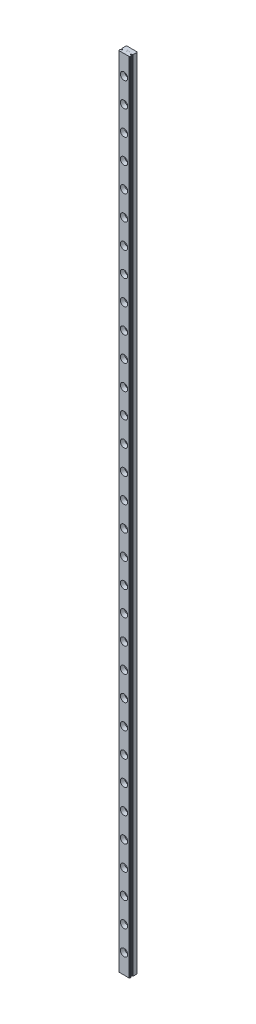
SolidWorks part; units mm, degrees
material "acero"
ref_plane "Alzado" through (0, 0, 0) normal (0, 0, 1) x (1, 0, 0)
ref_plane "Planta" through (0, 0, 0) normal (0, 1, 0) x (1, 0, 0)
ref_plane "Vista lateral" through (0, 0, 0) normal (1, 0, 0) x (0, 0, -1)
ref_plane "Plano1" through (0, 0, 0) normal (0, -1, 0) x (1, 0, 0)
sketch "Croquis1" plane through (0, 0, 0) normal (0, -1, 0) x (1, 0, 0)
  line L0 (4.5, 0) -> (4.5, 6.0117)
  line L1 (4.5, 6.0117) -> (4.1, 6.5)
  line L2 (4.1, 6.5) -> (-4.1, 6.5)
  line L3 (-4.1, 6.5) -> (-4.5, 6.0117)
  line L4 (-4.5, 6.0117) -> (-4.5, 0)
  line L5 (-4.5, 0) -> (4.5, 0)
extrude "Saliente-Extruir1" add sketch "Croquis1" against normal blind 652
sketch "Croquis2" plane through (0, 652, 0) normal (0, 1, 0) x (-1, 0, 0)
  line L0 (-4.5, 4.8802) -> (-4.5, 4.0315)
  line L1 (-4.5, 4.0315) -> (-3.8193, 4.0315)
  line L2 (-3.8193, 4.8802) -> (-4.5, 4.8802)
  arc A1 (-3.8193, 4.0315) -> (-3.8193, 4.8802) centre (-3.6695, 4.4558) ccw
  dimension "D4" = 0.9
  dimension "D2" = 0.8487
extrude "Cortar-Extruir1" cut sketch "Croquis2" against normal through all
sketch "Croquis3" plane through (0, 652, 0) normal (0, 1, 0) x (-1, 0, 0)
  line L0 (-4.0265, 4.0315) -> (-4.5, 4.0315)
  line L1 (-4.5, 4.0315) -> (-4.5, 3.5836)
  arc A0 (-4.5, 3.5836) -> (-4.0265, 4.0315) centre (-4.8765, 4.4558) ccw
extrude "Cortar-Extruir2" cut sketch "Croquis3" against normal through all
sketch "Croquis4" plane through (0, 652, 0) normal (0, 1, 0) x (-1, 0, 0)
  line L0 (-4.5, 5.3281) -> (-4.5, 4.8802)
  line L1 (-4.5, 4.8802) -> (-4.0265, 4.8802)
  arc A0 (-4.0265, 4.8802) -> (-4.5, 5.3281) centre (-4.8765, 4.4558) ccw
extrude "Cortar-Extruir3" cut sketch "Croquis4" against normal through all
sketch "Croquis5" plane through (0, 652, 0) normal (0, 1, 0) x (-1, 0, 0)
  line L0 (4.5, 4.0315) -> (4.5, 4.8802)
  line L1 (4.5, 4.8802) -> (3.8193, 4.8802)
  line L2 (3.8193, 4.0315) -> (4.5, 4.0315)
  arc A1 (3.8193, 4.8802) -> (3.8193, 4.0315) centre (3.6695, 4.4558) ccw
  dimension "D3" = 0.9
  dimension "D2" = 0.8487
extrude "Cortar-Extruir4" cut sketch "Croquis5" against normal through all
sketch "Croquis6" plane through (0, 652, 0) normal (0, 1, 0) x (-1, 0, 0)
  line L0 (4.0265, 4.8802) -> (4.5, 4.8802)
  line L1 (4.5, 4.8802) -> (4.5, 5.3281)
  arc A0 (4.5, 5.3281) -> (4.0265, 4.8802) centre (4.8765, 4.4558) ccw
extrude "Cortar-Extruir5" cut sketch "Croquis6" against normal through all
sketch "Croquis7" plane through (0, 652, 0) normal (0, 1, 0) x (-1, 0, 0)
  line L0 (4.5, 3.5836) -> (4.5, 4.0315)
  line L1 (4.5, 4.0315) -> (4.0265, 4.0315)
  arc A0 (4.0265, 4.0315) -> (4.5, 3.5836) centre (4.8765, 4.4558) ccw
extrude "Cortar-Extruir6" cut sketch "Croquis7" against normal through all
sketch "Croquis8" plane through (0, 652, 0) normal (0, 1, 0) x (-1, 0, 0)
  line L0 (0.8914, 3.4037) -> (0.7147, 3.1682)
  line L1 (0.7147, 3.1682) -> (0.2187, 2.611)
  line L2 (0.2187, 2.611) -> (1.0946, 2.6111)
  line L3 (1.0946, 2.6111) -> (1.0946, 2.696)
  line L4 (1.0946, 2.696) -> (0.3987, 2.696)
  line L5 (0.3987, 2.696) -> (0.7943, 3.1495)
  line L6 (0.7943, 3.1495) -> (0.9743, 3.3891)
  line L7 (0.9743, 3.3891) -> (1.0671, 3.5734)
  line L8 (1.0671, 3.5734) -> (0.9541, 3.8023)
  line L9 (0.9541, 3.8023) -> (0.7877, 3.8851)
  line L10 (0.7877, 3.8851) -> (0.543, 3.8851)
  line L11 (0.543, 3.8851) -> (0.3754, 3.8036)
  line L12 (0.3754, 3.8036) -> (0.295, 3.6384)
  line L13 (0.295, 3.6384) -> (0.295, 3.562)
  line L14 (0.295, 3.562) -> (0.3813, 3.562)
  line L15 (0.3813, 3.562) -> (0.3813, 3.6318)
  line L16 (0.3813, 3.6318) -> (0.4377, 3.7436)
  line L17 (0.4377, 3.7436) -> (0.5496, 3.8001)
  line L18 (0.5496, 3.8001) -> (0.7802, 3.8001)
  line L19 (0.7802, 3.8001) -> (0.893, 3.7438)
  line L20 (0.893, 3.7438) -> (0.9762, 3.576)
  line L21 (0.9762, 3.576) -> (0.8914, 3.4037)
extrude "Cortar-Extruir7" cut sketch "Croquis8" against normal blind 0.0022
sketch "Croquis9" plane through (0, 0, 0) normal (0, -1, 0) x (1, 0, 0)
  line L0 (-0.2146, 3.8851) -> (-0.954, 3.8851)
  line L1 (-0.954, 3.8851) -> (-0.954, 2.6111)
  line L2 (-0.954, 2.6111) -> (-0.2146, 2.6111)
  line L3 (-0.2146, 2.6111) -> (-0.2146, 2.696)
  line L4 (-0.2146, 2.696) -> (-0.869, 2.696)
  line L5 (-0.869, 2.696) -> (-0.869, 3.2056)
  line L6 (-0.869, 3.2056) -> (-0.5124, 3.2056)
  line L7 (-0.5124, 3.2056) -> (-0.5124, 3.2905)
  line L8 (-0.5124, 3.2905) -> (-0.869, 3.2905)
  line L9 (-0.869, 3.2905) -> (-0.869, 3.8001)
  line L10 (-0.869, 3.8001) -> (-0.2146, 3.8001)
  line L11 (-0.2146, 3.8001) -> (-0.2146, 3.8851)
extrude "Cortar-Extruir8" cut sketch "Croquis9" against normal blind 0.0022
sketch "Croquis10" plane through (0, 652, 0) normal (0, 1, 0) x (-1, 0, 0)
  line L0 (-0.2146, 3.8851) -> (-0.954, 3.8851)
  line L1 (-0.954, 3.8851) -> (-0.954, 2.6111)
  line L2 (-0.954, 2.6111) -> (-0.2146, 2.6111)
  line L3 (-0.2146, 2.6111) -> (-0.2146, 2.696)
  line L4 (-0.2146, 2.696) -> (-0.869, 2.696)
  line L5 (-0.869, 2.696) -> (-0.869, 3.2056)
  line L6 (-0.869, 3.2056) -> (-0.5124, 3.2056)
  line L7 (-0.5124, 3.2056) -> (-0.5124, 3.2905)
  line L8 (-0.5124, 3.2905) -> (-0.869, 3.2905)
  line L9 (-0.869, 3.2905) -> (-0.869, 3.8001)
  line L10 (-0.869, 3.8001) -> (-0.2146, 3.8001)
  line L11 (-0.2146, 3.8001) -> (-0.2146, 3.8851)
extrude "Cortar-Extruir9" cut sketch "Croquis10" against normal blind 0.0022
sketch "Croquis11" plane through (0, 0, 0) normal (0, -1, 0) x (1, 0, 0)
  line L0 (0.5101, 3.6208) -> (0.6071, 3.7187)
  line L1 (0.6071, 3.7187) -> (0.6071, 2.6094)
  line L2 (0.6071, 2.6094) -> (0.692, 2.6094)
  line L3 (0.692, 2.6094) -> (0.692, 3.8834)
  line L4 (0.692, 3.8834) -> (0.6741, 3.8834)
  line L5 (0.6741, 3.8834) -> (0.6741, 3.7951)
  line L6 (0.6741, 3.7951) -> (0.3691, 3.6407)
  line L7 (0.3691, 3.6407) -> (0.3691, 3.5513)
  line L8 (0.3691, 3.5513) -> (0.5101, 3.6208)
extrude "Cortar-Extruir10" cut sketch "Croquis11" against normal blind 0.0022
draft "Ángulo de salida1" type of draft neutral plane draft angle 45.147 faces to draft 1 face at (0.6741, 0.0011, 3.8392) neutral plane through (0.692, 0.0022, 3.8834) neutral plane normal (0, 0, -1) parameters "D1"=45.147
chamfer "Chaflán1" distance 0.4 angle 45 2 edges at (4.5, 326, 0) (-4.5, 326, 0)
fillet "Redondeo1" radius 0.13 8 edges at (4.5, 326, 3.5836) (4.0265, 326, 4.0315) (-4.0265, 326, 4.0315) (-4.0265, 326, 4.8802) (-4.5, 326, 5.3281) (-4.5, 326, 3.5836) (4.5, 326, 5.3281) (4.0265, 326, 4.8802)
hole_wizard "Taladro roscado M3.5x0.61" positions "Croquis35" profile "Croquis34" tap size "M3.5x0.6" standard "Ansi Metric"
sketch "Croquis35" plane through (0, 0, 0) normal (0, 0, -1) x (-1, 0, 0)
  line L3 (0, -8.7858) -> (0, 652) construction
  line L5 (-4.1, 652) -> (4.1, 652) construction
  line L6 (-4.1, 0) -> (4.1, 0) construction
  point P39 (0, 16)
sketch "Croquis34" plane through (0, 16, 0) normal (1, 0, 0) x (0, 1, 0)
  line L0 (0, 0) -> (0, 8)
  line L1 (0, 8) -> (3, 8)
  line L2 (3, 8) -> (3, 3)
  line L3 (3, 3) -> (1.5, 3)
  line L4 (1.5, 3) -> (1.5, 0)
  line L5 (1.5, 0) -> (0, 0)
  line L10 (0, 8) -> (-3, 8) construction
  line L11 (0, -6.35) -> (0, 107.95) construction
  dimension "Diámetro de perforador para roscar" = 6
  dimension "Profundidad de perforador para roscar" = 8
  dimension "Diámetro mayor de rosca" = 3
  dimension "Profundidad de rosca" = 3
  dimension "Ángulo de perforador" = 180
sketch "Croquis37" plane through (0, 0, 6.5) normal (0, 0, 1) x (1, 0, 0)
  line L0 (0, -8.7858) -> (0, 652) construction
  line L1 (0, -8.7858) -> (0, 652) construction
  line L2 (4.1, 652) -> (-4.1, 652) construction
  point P2 (0, 636)
pattern_linear "MatrizL2" count 32 spacing 20 along (0, 1, 0) of "Taladro roscado M3.5x0.61"
